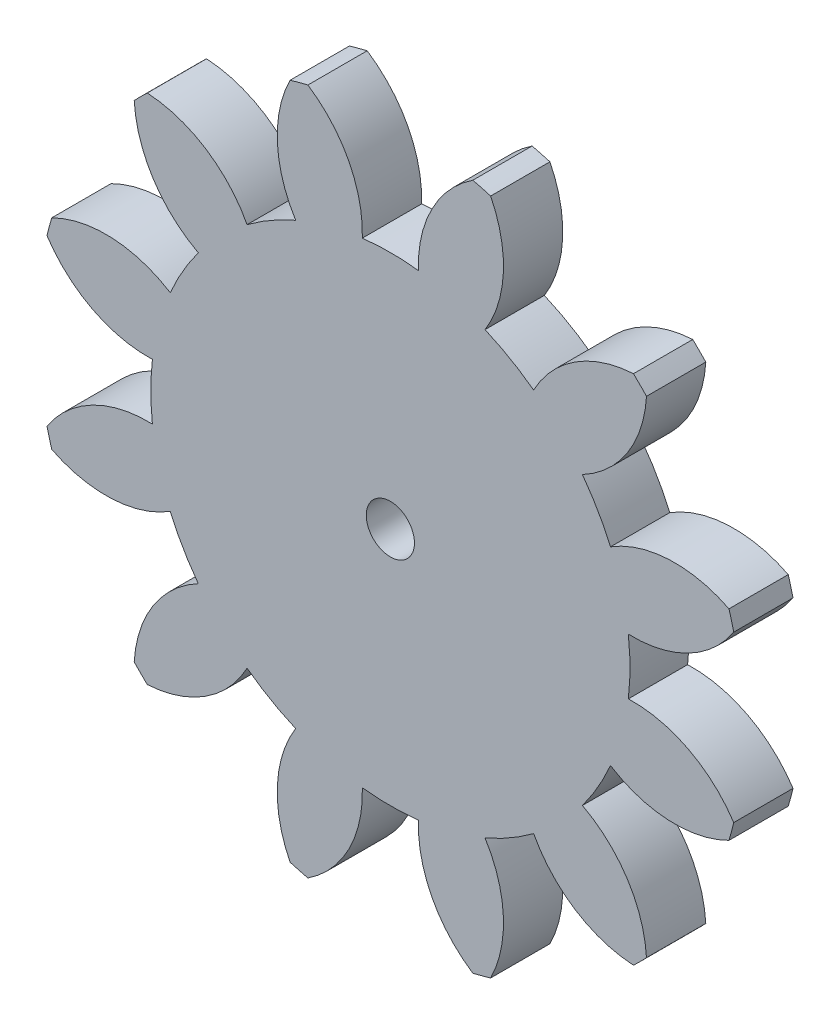
SolidWorks part; units mm, degrees
ref_plane "Front Plane" through (0, 0, 0) normal (0, 0, 1) x (1, 0, 0)
ref_plane "Top Plane" through (0, 0, 0) normal (0, 1, 0) x (1, 0, 0)
ref_plane "Right Plane" through (0, 0, 0) normal (1, 0, 0) x (0, 0, -1)
sketch "Sketch1" plane through (0, 0, 0) normal (0, 0, 1) x (1, 0, 0)
  arc A0 (31.0892, -0.0096) -> (27.1315, -2.5505) centre (31.371, -4.8013) ccw
  arc A1 (27.1315, -2.5505) -> (25.2056, -1.4386) centre (21.4517, -10.1644) ccw
  arc A2 (25.2056, -1.4386) -> (25.4272, 3.2593) centre (21.1366, 1.1075) ccw
  arc A3 (25.4272, 3.2593) -> (24.7206, 3.4487) centre (21.4517, -10.1644) ccw
  arc A4 (24.7206, 3.4487) -> (22.5636, -0.7307) centre (27.3606, -0.5602) ccw
  arc A5 (22.5636, -0.7307) -> (20.3398, -0.7307) centre (21.4517, -10.1644) ccw
  arc A6 (20.3398, -0.7307) -> (18.1828, 3.4487) centre (15.5428, -0.5602) ccw
  arc A7 (18.1828, 3.4487) -> (17.4762, 3.2593) centre (21.4517, -10.1644) ccw
  arc A8 (17.4762, 3.2593) -> (17.6978, -1.4386) centre (21.7669, 1.1075) ccw
  arc A9 (17.6978, -1.4386) -> (15.7719, -2.5505) centre (21.4517, -10.1644) ccw
  arc A10 (15.7719, -2.5505) -> (11.8142, -0.0096) centre (11.5324, -4.8013) ccw
  arc A11 (11.8142, -0.0096) -> (11.297, -0.5269) centre (21.4517, -10.1644) ccw
  arc A12 (11.297, -0.5269) -> (13.8378, -4.4846) centre (16.0887, -0.245) ccw
  arc A13 (13.8378, -4.4846) -> (12.7259, -6.4104) centre (21.4517, -10.1644) ccw
  arc A14 (12.7259, -6.4104) -> (8.028, -6.1888) centre (10.1798, -10.4795) ccw
  arc A15 (8.028, -6.1888) -> (7.8387, -6.8954) centre (21.4517, -10.1644) ccw
  arc A16 (7.8387, -6.8954) -> (12.018, -9.0524) centre (11.8475, -4.2555) ccw
  arc A17 (12.018, -9.0524) -> (12.018, -11.2763) centre (21.4517, -10.1644) ccw
  arc A18 (12.018, -11.2763) -> (7.8387, -13.4333) centre (11.8475, -16.0732) ccw
  arc A19 (7.8387, -13.4333) -> (8.028, -14.1399) centre (21.4517, -10.1644) ccw
  arc A20 (8.028, -14.1399) -> (12.7259, -13.9183) centre (10.1798, -9.8492) ccw
  arc A21 (12.7259, -13.9183) -> (13.8378, -15.8441) centre (21.4517, -10.1644) ccw
  arc A22 (13.8378, -15.8441) -> (11.297, -19.8018) centre (16.0887, -20.0837) ccw
  arc A23 (11.297, -19.8018) -> (11.8142, -20.3191) centre (21.4517, -10.1644) ccw
  arc A24 (11.8142, -20.3191) -> (15.7719, -17.7782) centre (11.5324, -15.5274) ccw
  arc A25 (15.7719, -17.7782) -> (17.6978, -18.8901) centre (21.4517, -10.1644) ccw
  arc A26 (17.6978, -18.8901) -> (17.4762, -23.588) centre (21.7669, -21.4363) ccw
  arc A27 (17.4762, -23.588) -> (18.1828, -23.7774) centre (21.4517, -10.1644) ccw
  arc A28 (18.1828, -23.7774) -> (20.3398, -19.5981) centre (15.5428, -19.7685) ccw
  arc A29 (20.3398, -19.5981) -> (22.5636, -19.5981) centre (21.4517, -10.1644) ccw
  arc A30 (22.5636, -19.5981) -> (24.7206, -23.7774) centre (27.3606, -19.7685) ccw
  arc A31 (24.7206, -23.7774) -> (25.4272, -23.588) centre (21.4517, -10.1644) ccw
  arc A32 (25.4272, -23.588) -> (25.2056, -18.8901) centre (21.1366, -21.4363) ccw
  arc A33 (25.2056, -18.8901) -> (27.1315, -17.7782) centre (21.4517, -10.1644) ccw
  arc A34 (27.1315, -17.7782) -> (31.0892, -20.3191) centre (31.371, -15.5274) ccw
  arc A35 (31.0892, -20.3191) -> (31.6064, -19.8018) centre (21.4517, -10.1644) ccw
  arc A36 (31.6064, -19.8018) -> (29.0656, -15.8441) centre (26.8147, -20.0837) ccw
  arc A37 (29.0656, -15.8441) -> (30.1775, -13.9183) centre (21.4517, -10.1644) ccw
  arc A38 (30.1775, -13.9183) -> (34.8754, -14.1399) centre (32.7236, -9.8492) ccw
  arc A39 (34.8754, -14.1399) -> (35.0647, -13.4333) centre (21.4517, -10.1644) ccw
  arc A40 (35.0647, -13.4333) -> (30.8854, -11.2763) centre (31.0559, -16.0732) ccw
  arc A41 (30.8854, -11.2763) -> (30.8854, -9.0524) centre (21.4517, -10.1644) ccw
  arc A42 (30.8854, -9.0524) -> (35.0647, -6.8954) centre (31.0559, -4.2555) ccw
  arc A43 (35.0647, -6.8954) -> (34.8754, -6.1888) centre (21.4517, -10.1644) ccw
  arc A44 (34.8754, -6.1888) -> (30.1775, -6.4104) centre (32.7236, -10.4795) ccw
  arc A45 (30.1775, -6.4104) -> (29.0656, -4.4846) centre (21.4517, -10.1644) ccw
  arc A46 (29.0656, -4.4846) -> (31.6064, -0.5269) centre (26.8147, -0.245) ccw
  arc A47 (31.6064, -0.5269) -> (31.0892, -0.0096) centre (21.4517, -10.1644) ccw
  circle A48 centre (21.4517, -10.1644) radius 0.955
  dimension "D1" = 1.91
extrude "Boss-Extrude1" add sketch "Sketch1" along normal blind 2.35
